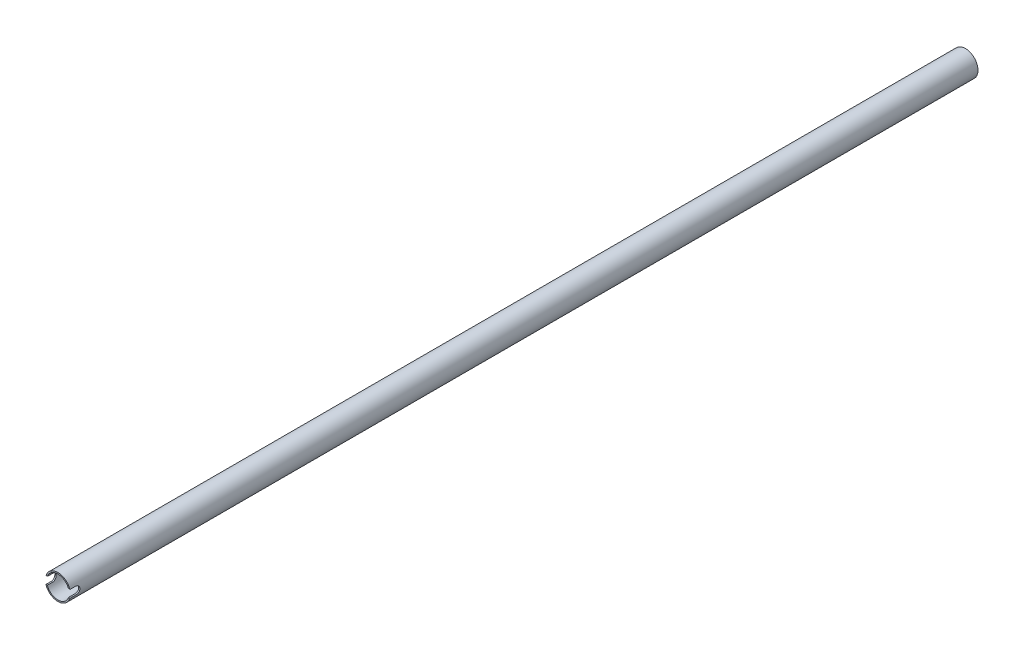
SolidWorks part; units mm, degrees
ref_plane "Front Plane" through (0, 0, 0) normal (0, 0, 1) x (1, 0, 0)
ref_plane "Top Plane" through (0, 0, 0) normal (0, 1, 0) x (1, 0, 0)
ref_plane "Right Plane" through (0, 0, 0) normal (1, 0, 0) x (0, 0, -1)
sketch "Sketch4" plane through (0, 0, 0) normal (0, 0, 1) x (1, 0, 0)
  line L0 (0, 0) -> (66, 0) construction
  circle A0 centre (33, 0) radius 33
  circle A1 centre (33, 0) radius 29.5
extrude "Boss-Extrude1" add sketch "Sketch4" against normal blind 2380
sketch "Sketch6" plane through (0, 0, 0) normal (1, 0, 0) x (0, 0, -1)
  line L0 (0, 10) -> (0, -10)
  line L1 (0, 33) -> (0, -33) construction
  line L2 (0, -10) -> (15, -10)
  line L3 (0, 10) -> (15, 10)
  arc A0 (15, 10) -> (15, -10) centre (15, 0) cw
  point P6 (0, 0)
extrude "Cut-Extrude1" cut sketch "Sketch6" along normal through all
fillet "Fillet1" radius 1 4 edges at (62.6009, -10, 0) (3.3991, -10, 0) (62.6009, 10, 0) (3.3991, 10, 0)
